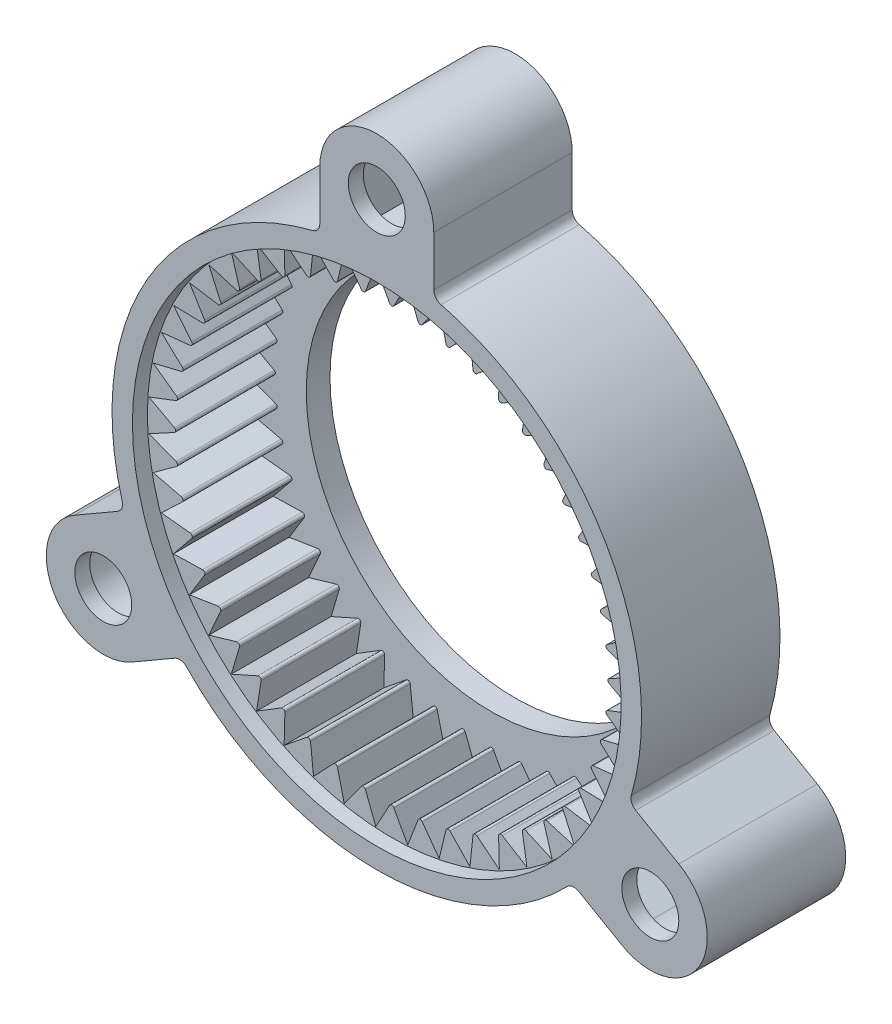
SolidWorks part; units mm, degrees
material "PE Low/Medium Density"
ref_plane "Front Plane" through (0, 0, 0) normal (0, 0, 1) x (1, 0, 0)
ref_plane "Top Plane" through (0, 0, 0) normal (0, 1, 0) x (1, 0, 0)
ref_plane "Right Plane" through (0, 0, 0) normal (1, 0, 0) x (0, 0, -1)
sketch "Sketch1" plane through (0, 0, 0) normal (1, 0, 0) x (0, 0, -1)
  line L0 (0, 14.1605) -> (0, 13.0683)
  line L1 (7.4041, 14.1605) -> (7.4041, 12.8905)
  line L2 (0, 0) -> (0, 14.9151) construction
  line L3 (0, 14.1605) -> (7.4041, 14.1605)
  line L4 (7.9756, 12.2301) -> (7.9756, 12.8905)
  line L5 (0, 0) -> (-0.9535, 0) construction
  line L6 (7.4041, 12.2301) -> (7.4041, 9.906)
  line L7 (7.4041, 12.8905) -> (7.9756, 12.8905)
  line L8 (-0.9535, 0) -> (10.0571, 0) construction
  line L9 (7.9756, 12.2301) -> (7.4041, 12.2301)
  line L12 (7.4041, 9.906) -> (6.1341, 9.906)
  line L13 (6.1341, 9.906) -> (6.1341, 13.0683)
  line L14 (6.1341, 13.0683) -> (0, 13.0683)
  dimension "D1" = 14.1605
  dimension "D2" = 9.906
  dimension "D3" = 0.5715
  dimension "D4" = 1.27
  dimension "D5" = 1.0922
  dimension "D6" = 6.1341
  dimension "D7" = 0.6604
  dimension "D8" = 1.27
revolve "Base revolve" add sketch "Sketch1" angle 360 about L5
sketch "Sketch3" plane through (0, 0, -7.4041) normal (0, 0, -1) x (-1, 0, 0)
  line L0 (-3.048, 16.891) -> (-3.048, 13.8286)
  line L1 (3.048, 16.891) -> (3.048, 13.8286)
  line L2 (0, 0) -> (0, 22.6145) construction
  arc A0 (3.048, 16.891) -> (-3.048, 16.891) centre (0, 16.891) ccw
  circle A1 centre (0, 0) radius 14.1605 construction
  circle A2 centre (0, 16.891) radius 1.524
  arc A3 (-3.048, 13.8286) -> (3.048, 13.8286) centre (0, 0) cw
  point P12 (0, 19.939)
  dimension "D1" = 3.048
  dimension "D2" = 3.048
  dimension "D3" = 16.891
extrude "Mount" add sketch "Sketch3" against normal up to surface (7.4041 mm away) up to face at (-13.0683, 0, 0)
sketch "Sketch7" plane through (0, 0, -7.4041) normal (0, 0, -1) x (-1, 0, 0)
  line L0 (-2.032, 16.891) -> (-2.032, 14.0139)
  line L1 (2.032, 16.891) -> (2.032, 14.0139)
  line L2 (-3.048, 16.891) -> (-3.048, 13.8286) construction
  arc A0 (2.032, 14.0139) -> (-2.032, 14.0139) centre (0, 0) ccw
  arc A1 (2.032, 16.891) -> (-2.032, 16.891) centre (0, 16.891) ccw
  arc A3 (-3.048, 13.8286) -> (3.048, 13.8286) centre (0, 0) ccw construction
  dimension "D1" = 1.016
extrude "Shelling of mount" cut sketch "Sketch7" against normal blind 6.604
pattern_circular "Circular pattern for mounts" count 3 over 360 about axis through (0, 0, 0) along (0, 0, 1) of "Mount", "Shelling of mount"
fillet "Touch-up fillets" radius 0.508 6 edges at (-3.048, 13.8286, -3.702) (-13.4999, -4.2746, -3.702) (-10.4519, -9.5539, -3.702) (10.4519, -9.5539, -3.702) (13.4999, -4.2746, -3.702) (3.048, 13.8286, -3.702)
sketch "Sketch8" plane through (0, 0, -6.1341) normal (0, 0, 1) x (1, 0, 0)
  line L0 (0, 0) -> (0, 13.0683) construction
  line L1 (-0.1116, 11.6234) -> (-0.9906, 13.2408)
  line L2 (0, 13.2408) -> (0, 13.0683) construction
  line L3 (0.9906, 13.2408) -> (-0.9906, 13.2408)
  line L4 (0.1116, 11.6234) -> (0.9906, 13.2408)
  circle A0 centre (0, 0) radius 13.0683 construction
  arc A2 (0.1116, 11.6234) -> (-0.1116, 11.6234) centre (0, 11.684) cw
  dimension "D3" = 0.127
  dimension "D1" = 0.9906
  dimension "D2" = 1.5568
  dimension "D4" = 11.684
extrude "Tooth" add sketch "Sketch8" along normal blind 5.334
pattern_circular "Pattern for teeth" count 48 over 360 about axis through (0, 0, 0) along (0, 0, 1) of "Tooth"
